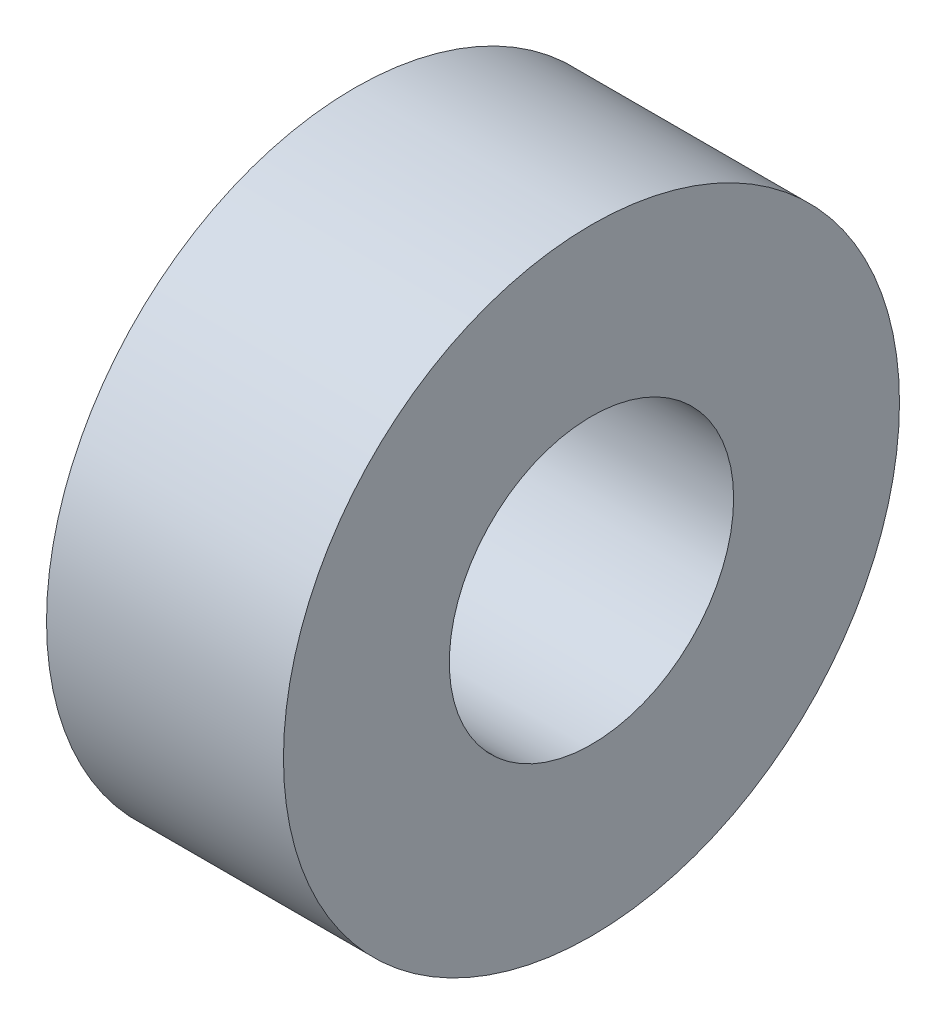
SolidWorks part; units mm, degrees
ref_plane "前视基准面" through (0, 0, 0) normal (0, 0, 1) x (1, 0, 0)
ref_plane "上视基准面" through (0, 0, 0) normal (0, 1, 0) x (1, 0, 0)
ref_plane "右视基准面" through (0, 0, 0) normal (1, 0, 0) x (0, 0, -1)
sketch "草图1" plane through (0, 0, 0) normal (1, 0, 0) x (0, 0, -1)
  circle A0 centre (0, 0) radius 6.5
  circle A1 centre (0, 0) radius 3
extrude "凸台-拉伸1" add sketch "草图1" along normal blind 5
